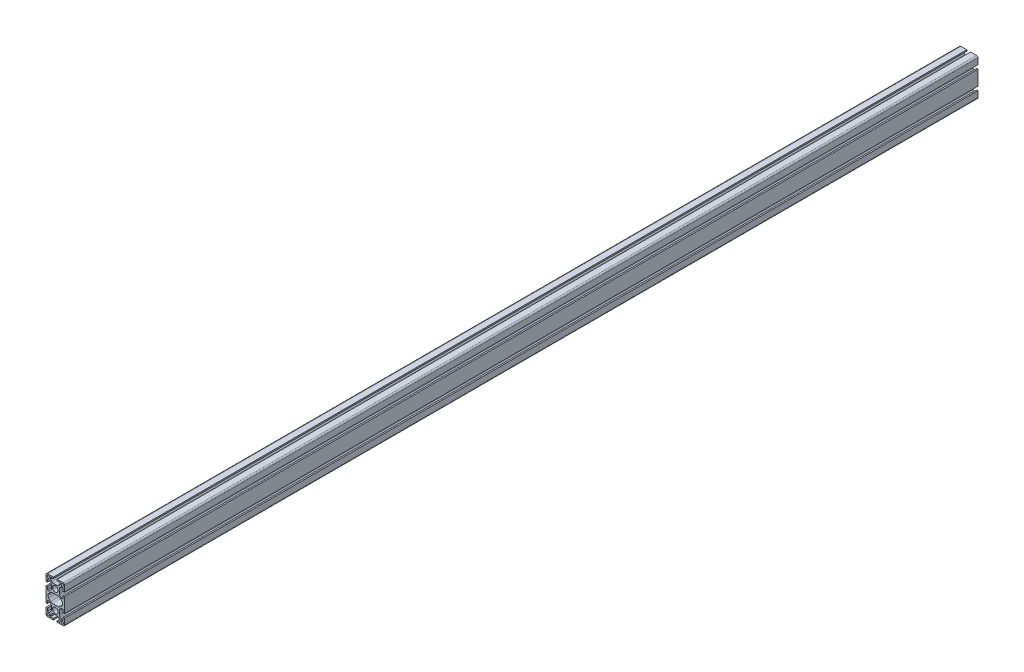
SolidWorks part; units mm, degrees
ref_plane "Front Plane" through (0, 0, 0) normal (0, 0, 1) x (1, 0, 0)
ref_plane "Top Plane" through (0, 0, 0) normal (0, 1, 0) x (1, 0, 0)
ref_plane "Right Plane" through (0, 0, 0) normal (1, 0, 0) x (0, 0, -1)
sketch "Sketch1" plane through (0, 0, 0) normal (0, 0, 1) x (1, 0, 0)
  line L0 (-17, -40) -> (-4.1, -40)
  line L1 (-4.1, -40) -> (-4.1, -37)
  line L2 (-4.1, -37) -> (-10.5, -37)
  line L3 (-10.5, -37) -> (-10.5, -33.6627)
  line L4 (-10.0314, -32.5314) -> (-7.4645, -29.9645)
  line L5 (-3.9289, -28.5) -> (3.9289, -28.5)
  line L6 (7.4645, -29.9645) -> (10.0314, -32.5314)
  line L7 (10.5, -33.6627) -> (10.5, -37)
  line L8 (10.5, -37) -> (4.1, -37)
  line L9 (4.1, -37) -> (4.1, -40)
  line L10 (4.1, -40) -> (17, -40)
  line L11 (20, -37) -> (20, -24.1)
  line L12 (20, -24.1) -> (17, -24.1)
  line L13 (17, -24.1) -> (17, -30.5)
  line L14 (17, -30.5) -> (13.6627, -30.5)
  line L15 (12.5314, -30.0314) -> (9.9645, -27.4645)
  line L16 (8.5, -23.9289) -> (8.5, -16.0711)
  line L17 (9.9645, -12.5355) -> (12.5314, -9.9686)
  line L18 (13.6627, -9.5) -> (17, -9.5)
  line L19 (17, -9.5) -> (17, -15.9)
  line L20 (17, -15.9) -> (20, -15.9)
  line L21 (20, -15.9) -> (20, 15.9)
  line L22 (20, 15.9) -> (17, 15.9)
  line L23 (17, 15.9) -> (17, 9.5)
  line L24 (17, 9.5) -> (13.6627, 9.5)
  line L25 (12.5314, 9.9686) -> (9.9645, 12.5355)
  line L26 (8.5, 16.0711) -> (8.5, 23.9289)
  line L27 (9.9645, 27.4645) -> (12.5314, 30.0314)
  line L28 (13.6627, 30.5) -> (17, 30.5)
  line L29 (17, 30.5) -> (17, 24.1)
  line L30 (17, 24.1) -> (20, 24.1)
  line L31 (20, 24.1) -> (20, 37)
  line L32 (17, 40) -> (4.1, 40)
  line L33 (4.1, 40) -> (4.1, 37)
  line L34 (4.1, 37) -> (10.5, 37)
  line L35 (10.5, 37) -> (10.5, 33.6627)
  line L36 (10.0314, 32.5314) -> (7.4645, 29.9645)
  line L37 (3.9289, 28.5) -> (-3.9289, 28.5)
  line L38 (-7.4645, 29.9645) -> (-10.0314, 32.5314)
  line L39 (-10.5, 33.6627) -> (-10.5, 37)
  line L40 (-10.5, 37) -> (-4.1, 37)
  line L41 (-4.1, 37) -> (-4.1, 40)
  line L42 (-4.1, 40) -> (-17, 40)
  line L43 (-20, 37) -> (-20, 24.1)
  line L44 (-20, 24.1) -> (-17, 24.1)
  line L45 (-17, 24.1) -> (-17, 30.5)
  line L46 (-17, 30.5) -> (-13.6627, 30.5)
  line L47 (-12.5314, 30.0314) -> (-9.9645, 27.4645)
  line L48 (-8.5, 23.9289) -> (-8.5, 16.0711)
  line L49 (-9.9645, 12.5355) -> (-12.5314, 9.9686)
  line L50 (-13.6627, 9.5) -> (-17, 9.5)
  line L51 (-17, 9.5) -> (-17, 15.9)
  line L52 (-17, 15.9) -> (-20, 15.9)
  line L53 (-20, 15.9) -> (-20, -15.9)
  line L54 (-20, -15.9) -> (-17, -15.9)
  line L55 (-17, -15.9) -> (-17, -9.5)
  line L56 (-17, -9.5) -> (-13.6627, -9.5)
  line L57 (-12.5314, -9.9686) -> (-9.9645, -12.5355)
  line L58 (-8.5, -16.0711) -> (-8.5, -23.9289)
  line L59 (-9.9645, -27.4645) -> (-12.5314, -30.0314)
  line L60 (-13.6627, -30.5) -> (-17, -30.5)
  line L61 (-17, -30.5) -> (-17, -24.1)
  line L62 (-17, -24.1) -> (-20, -24.1)
  line L63 (-20, -24.1) -> (-20, -37)
  line L64 (-14.2426, -4.2426) -> (-9.9497, -8.5355)
  line L65 (-6.4142, -10) -> (6.4142, -10)
  line L66 (9.9497, -8.5355) -> (14.2426, -4.2426)
  line L67 (14.2426, 4.2426) -> (9.9497, 8.5355)
  line L68 (6.4142, 10) -> (-6.4142, 10)
  line L69 (-9.9497, 8.5355) -> (-14.2426, 4.2426)
  arc A0 (-20, -37) -> (-17, -40) centre (-17, -37) ccw
  arc A1 (-10.5, -33.6627) -> (-10.0314, -32.5314) centre (-8.9, -33.6627) cw
  arc A2 (-7.4645, -29.9645) -> (-3.9289, -28.5) centre (-3.9289, -33.5) cw
  arc A3 (3.9289, -28.5) -> (7.4645, -29.9645) centre (3.9289, -33.5) cw
  arc A4 (10.0314, -32.5314) -> (10.5, -33.6627) centre (8.9, -33.6627) cw
  arc A5 (17, -40) -> (20, -37) centre (17, -37) ccw
  arc A6 (13.6627, -30.5) -> (12.5314, -30.0314) centre (13.6627, -28.9) cw
  arc A7 (9.9645, -27.4645) -> (8.5, -23.9289) centre (13.5, -23.9289) cw
  arc A8 (8.5, -16.0711) -> (9.9645, -12.5355) centre (13.5, -16.0711) cw
  arc A9 (12.5314, -9.9686) -> (13.6627, -9.5) centre (13.6627, -11.1) cw
  arc A10 (13.6627, 9.5) -> (12.5314, 9.9686) centre (13.6627, 11.1) cw
  arc A11 (9.9645, 12.5355) -> (8.5, 16.0711) centre (13.5, 16.0711) cw
  arc A12 (8.5, 23.9289) -> (9.9645, 27.4645) centre (13.5, 23.9289) cw
  arc A13 (12.5314, 30.0314) -> (13.6627, 30.5) centre (13.6627, 28.9) cw
  arc A14 (20, 37) -> (17, 40) centre (17, 37) ccw
  arc A15 (10.5, 33.6627) -> (10.0314, 32.5314) centre (8.9, 33.6627) cw
  arc A16 (7.4645, 29.9645) -> (3.9289, 28.5) centre (3.9289, 33.5) cw
  arc A17 (-3.9289, 28.5) -> (-7.4645, 29.9645) centre (-3.9289, 33.5) cw
  arc A18 (-10.0314, 32.5314) -> (-10.5, 33.6627) centre (-8.9, 33.6627) cw
  arc A19 (-17, 40) -> (-20, 37) centre (-17, 37) ccw
  arc A20 (-13.6627, 30.5) -> (-12.5314, 30.0314) centre (-13.6627, 28.9) cw
  arc A21 (-9.9645, 27.4645) -> (-8.5, 23.9289) centre (-13.5, 23.9289) cw
  arc A22 (-8.5, 16.0711) -> (-9.9645, 12.5355) centre (-13.5, 16.0711) cw
  arc A23 (-12.5314, 9.9686) -> (-13.6627, 9.5) centre (-13.6627, 11.1) cw
  arc A24 (-13.6627, -9.5) -> (-12.5314, -9.9686) centre (-13.6627, -11.1) cw
  arc A25 (-9.9645, -12.5355) -> (-8.5, -16.0711) centre (-13.5, -16.0711) cw
  arc A26 (-8.5, -23.9289) -> (-9.9645, -27.4645) centre (-13.5, -23.9289) cw
  arc A27 (-12.5314, -30.0314) -> (-13.6627, -30.5) centre (-13.6627, -28.9) cw
  circle A28 centre (15, 35) radius 2.5
  circle A29 centre (15, -35) radius 2.5
  circle A30 centre (0, 20) radius 6
  circle A31 centre (0, -20) radius 6
  arc A32 (-14.2426, 4.2426) -> (-14.2426, -4.2426) centre (-10, 0) ccw
  arc A33 (-9.9497, -8.5355) -> (-6.4142, -10) centre (-6.4142, -5) ccw
  arc A34 (6.4142, -10) -> (9.9497, -8.5355) centre (6.4142, -5) ccw
  arc A35 (14.2426, -4.2426) -> (14.2426, 4.2426) centre (10, 0) ccw
  arc A36 (9.9497, 8.5355) -> (6.4142, 10) centre (6.4142, 5) ccw
  arc A37 (-6.4142, 10) -> (-9.9497, 8.5355) centre (-6.4142, 5) ccw
  circle A38 centre (-15, 35) radius 2.5
  circle A39 centre (-15, -35) radius 2.5
  dimension "D1" = 40
  dimension "D2" = 80
extrude "Boss-Extrude1" add sketch "Sketch1" against normal blind 1964
